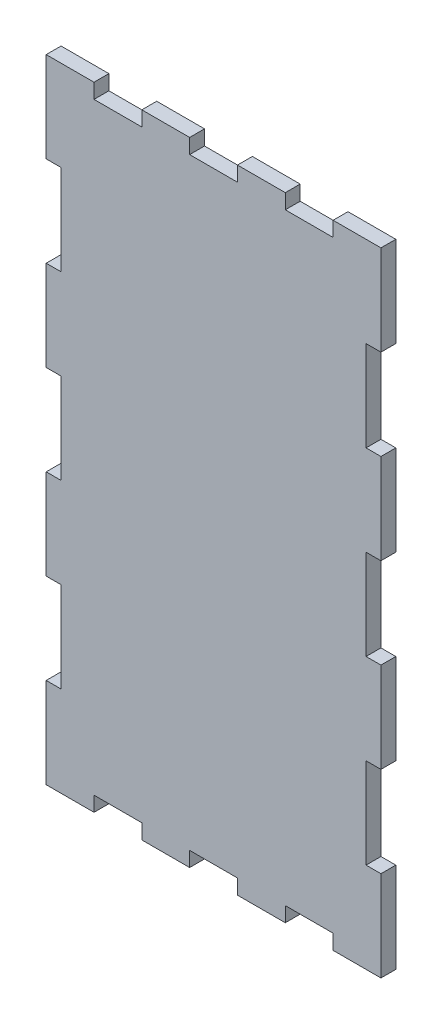
SolidWorks part; units mm, degrees
ref_plane "Front Plane" through (0, 0, 0) normal (0, 0, 1) x (1, 0, 0)
ref_plane "Top Plane" through (0, 0, 0) normal (0, 1, 0) x (1, 0, 0)
ref_plane "Right Plane" through (0, 0, 0) normal (1, 0, 0) x (0, 0, -1)
sketch "Buitenafmeting Rechthoek" plane through (0, 0, 0) normal (0, 0, 1) x (1, 0, 0)
  line L1 (0, 0) -> (90, 0)
  line L2 (0, 0) -> (0, 170)
  line L3 (0, 170) -> (90, 170)
  line L4 (90, 0) -> (90, 170)
  dimension "D1" = 90
  dimension "D2" = 170
extrude "Plaat" add sketch "Buitenafmeting Rechthoek" against normal blind 4
sketch "Tand Hor" plane through (0, 0, 0) normal (0, 0, 1) x (1, 0, 0)
  line L1 (90, 170) -> (0, 170) construction
  line L2 (12.8571, 170) -> (25.7143, 170)
  line L3 (12.8571, 170) -> (12.8571, 166)
  line L4 (12.8571, 166) -> (25.7143, 166)
  line L6 (25.7143, 170) -> (25.7143, 166)
  dimension "D1" = 4
  dimension "D2" = 12.8571
  dimension "D3" = 12.8571
extrude "Tand Boven" cut sketch "Tand Hor" against normal through all
pattern_linear "Tanden Patroon Boven" count 3 spacing 25.7143 along (1, 0, 0) of "Tand Boven"
sketch "Tand Ver" plane through (0, 0, 0) normal (0, 0, 1) x (1, 0, 0)
  line L0 (0, 170) -> (0, 0) construction
  line L1 (0, 145.7143) -> (4, 145.7143)
  line L2 (0, 145.7143) -> (0, 121.4286)
  line L3 (0, 121.4286) -> (4, 121.4286)
  line L4 (4, 145.7143) -> (4, 121.4286)
  dimension "D1" = 4
  dimension "D2" = 24.2857
  dimension "D3" = 145.7143
extrude "Tand Links" cut sketch "Tand Ver" against normal through all
pattern_linear "Tanden Patroon Links" count 3 spacing 48.5714 along (0, -1, 0) of "Tand Links"
sketch "Tand O" plane through (0, 0, 0) normal (0, 0, 1) x (1, 0, 0)
  line L0 (0, 0) -> (90, 0) construction
  line L1 (12.8571, 0) -> (25.7143, 0)
  line L2 (12.8571, 0) -> (12.8571, 4)
  line L3 (12.8571, 4) -> (25.7143, 4)
  line L4 (25.7143, 0) -> (25.7143, 4)
  dimension "D1" = 4
  dimension "D2" = 12.8571
  dimension "D3" = 12.8571
extrude "Tand Onder" cut sketch "Tand O" against normal through all
pattern_linear "Tanden Patroon Onder" count 3 spacing 25.7143 along (1, 0, 0) of "Tand Onder"
sketch "Tand R" plane through (0, 0, 0) normal (0, 0, 1) x (1, 0, 0)
  line L0 (90, 0) -> (90, 170) construction
  line L1 (90, 145.7143) -> (86, 145.7143)
  line L2 (90, 145.7143) -> (90, 121.4286)
  line L3 (90, 121.4286) -> (86, 121.4286)
  line L4 (86, 145.7143) -> (86, 121.4286)
  dimension "D1" = 4
  dimension "D2" = 24.2857
  dimension "D3" = 145.7143
extrude "Tand Rechts" cut sketch "Tand R" against normal through all
pattern_linear "Tanden Patroon Rechts" count 3 spacing 48.5714 along (0, -1, 0) of "Tand Rechts"
equation "\"D1@Buitenafmeting Rechthoek\"= \"Lengte\""
equation "\"D2@Buitenafmeting Rechthoek\" = \"Hoogte\""
equation "\"D1@Plaat\" = \"Dikte\""
equation "\"D3@Tanden Patroon Boven\" = \"LengteHorTand\" * 2"
equation "\"D1@Tanden Patroon Boven\" = \"nPatroonHor\""
equation "\"LengteHorTand\"= \"Lengte\" / \"nHor\"'Spatie tussen verschillende tanden in de lengte"
equation "\"nPatroonHor\"= ( \"nHor\" + 1 ) / 2 - \"GrensHor\"'Aantal kopies van tanden in de lengte"
equation "\"D1@Tand Hor\" = \"Dikte\""
equation "\"D2@Tand Hor\" = \"LengteHorTand\""
equation "\"D1@Tand Ver\" = \"Dikte\""
equation "\"LengteVertTand\"= \"Hoogte\" / \"nVert\"'Spatie tussen verschillende tanden in de hoogte"
equation "\"nPatroonVert\"= ( \"nVert\" + 1 ) / 2 - \"GrensVert\"'Aantal kopies van tanden in de hoogte"
equation "\"D2@Tand Ver\"=\"LengteVertTand\""
equation "\"D3@Tanden Patroon Links\"=\"LengteVertTand\"*2"
equation "\"D3@Tanden Patroon Rechts\"=\"LengteVertTand\"*2"
equation "\"D1@Tanden Patroon Rechts\"=\"nPatroonVert\""
equation "\"D3@Tanden Patroon Onder\"=\"LengteHorTand\"*2"
equation "\"D1@Tanden Patroon Onder\"=\"nPatroonHor\""
equation "\"D1@Tanden Patroon Links\"=\"nPatroonVert\""
equation "\"D3@Tand Ver\"=\"Hoogte\"-\"GrensVert\"*\"LengteVertTand\""
equation "\"D2@Tand R\" = \"LengteVertTand\""
equation "\"D3@Tand R\" = \"Hoogte\" - \"GrensVert\" * \"LengteVertTand\""
equation "\"D2@Tand O\"=\"LengteHorTand\""
equation "\"D3@Tand Hor\"=\"GrensHor\"*\"LengteHorTand\""
equation "\"D3@Tand O\"=\"GrensHor\"*\"LengteHorTand\""
equation "\"Tand Boven\"= IIF ( \"plaatsTandenBoven\" , \"unsuppressed\" , \"suppressed\" )"
equation "\"Tanden Patroon Boven\"= IIF ( \"plaatsTandenBoven\" , \"unsuppressed\" , \"suppressed\" )"
equation "\"Tand Links\"= IIF ( \"plaatsTandenLinks\" , \"unsuppressed\" , \"suppressed\" )"
equation "\"Tanden Patroon Links\"= IIF ( \"plaatsTandenLinks\" , \"unsuppressed\" , \"suppressed\" )"
equation "\"Tand Onder\"= IIF ( \"plaatsTandenOnder\" , \"unsuppressed\" , \"suppressed\" )"
equation "\"Tanden Patroon Onder\"= IIF ( \"plaatsTandenOnder\" , \"unsuppressed\" , \"suppressed\" )"
equation "\"Tand Rechts\"= IIF ( \"plaatsTandenRechts\" , \"unsuppressed\" , \"suppressed\" )"
equation "\"Tanden Patroon Rechts\"= IIF ( \"plaatsTandenRechts\" , \"unsuppressed\" , \"suppressed\" )"
equation "\"D1@Tand O\"=\"Dikte\""
equation "\"D1@Tand R\"=\"Dikte\""
